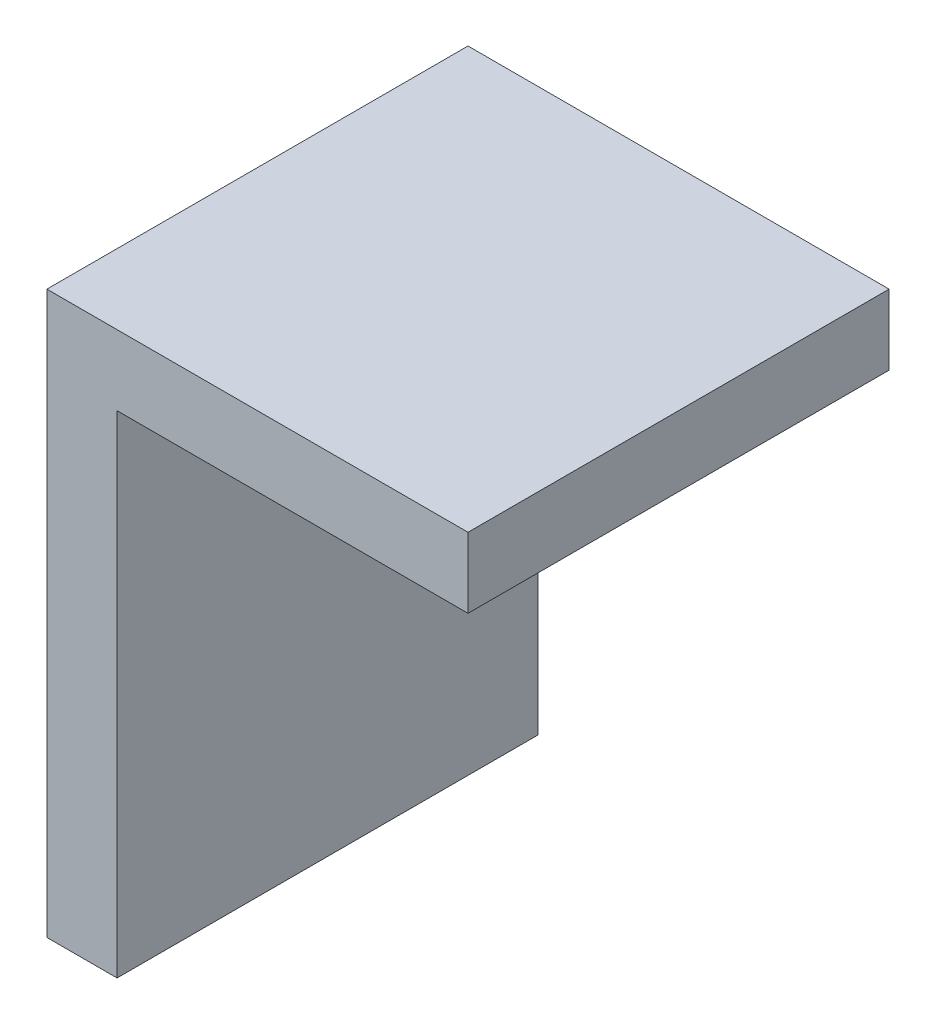
SolidWorks part; units mm, degrees
ref_plane "Plan de face" through (0, 0, 0) normal (0, 0, 1) x (1, 0, 0)
ref_plane "Plan de dessus" through (0, 0, 0) normal (0, 1, 0) x (1, 0, 0)
ref_plane "Plan de droite" through (0, 0, 0) normal (1, 0, 0) x (0, 0, -1)
sketch "Esquisse1" plane through (0, 0, 0) normal (0, 0, 1) x (1, 0, 0)
  line L1 (-22.0192, 15.9183) -> (-17.0192, 15.9183)
  line L2 (-22.0192, 15.9183) -> (-22.0192, -19.0817)
  line L3 (-22.0192, -19.0817) -> (-17.0192, -19.0817)
  line L4 (-17.0192, 15.9183) -> (-17.0192, -19.0817)
  line L5 (-22.0192, 15.9183) -> (7.9808, 15.9183)
  line L6 (-22.0192, 15.9183) -> (-22.0192, 20.9183)
  line L7 (-22.0192, 20.9183) -> (7.9808, 20.9183)
  line L8 (7.9808, 15.9183) -> (7.9808, 20.9183)
  dimension "D1" = 35
  dimension "D2" = 5
  dimension "D3" = 30
  dimension "D4" = 5
extrude "Boss.-Extru.2" add sketch "Esquisse1" along normal blind 30 contours L4 L1 L2 L3 | L5 L8 L7 L6
